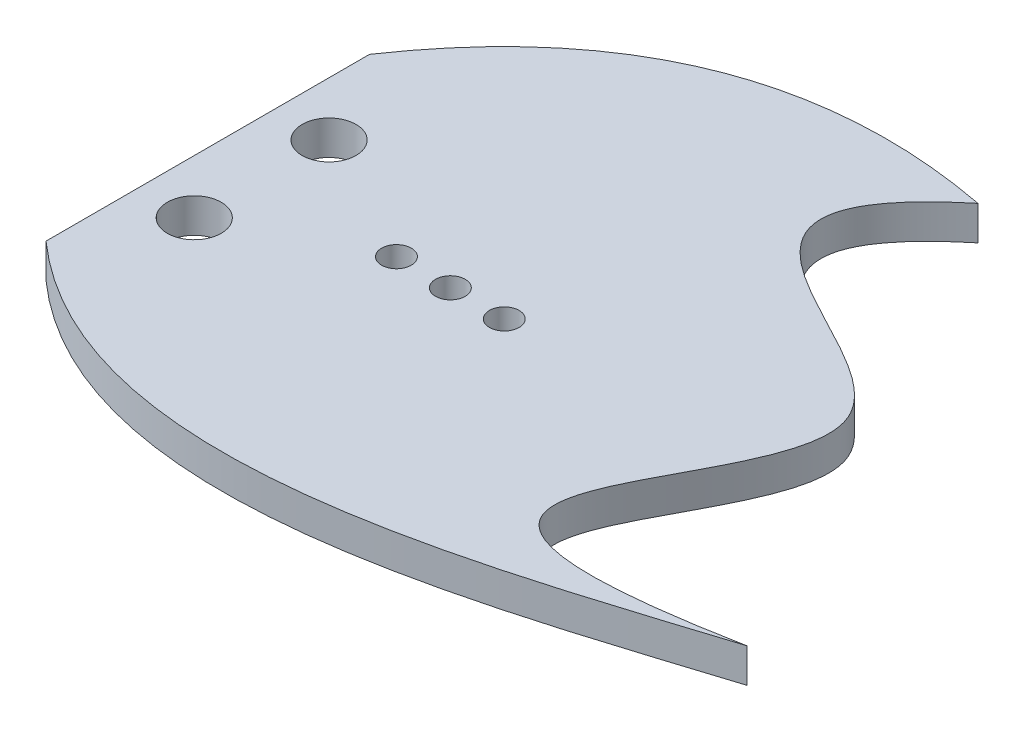
SolidWorks part; units mm, degrees
ref_plane "Front Plane" through (0, 0, 0) normal (0, 0, 1) x (1, 0, 0)
ref_plane "Top Plane" through (0, 0, 0) normal (0, 1, 0) x (1, 0, 0)
ref_plane "Right Plane" through (0, 0, 0) normal (1, 0, 0) x (0, 0, -1)
sketch "Sketch2" plane through (0, 0, 0) normal (0, 1, 0) x (1, 0, 0)
  line L0 (56.3918, 108.1514) -> (56.3918, 48.1514)
  spline S0 degree 2 poles (56.3918, 108.1514) (85.0564, 150.5532) (136.7606, 140.646) knots 0 0 0 1 1 1
  spline S1 degree 3 poles (56.3918, 48.1514) (92.6532, 15.9657) (146.2241, 35.5513) (186.3918, 48.1514) knots 0 0 0 0 1 1 1 1
  spline S2 degree 3 poles (186.3918, 48.1514) (110.317, 33.4597) (213.9084, 108.5176) (101.7916, 111.9077) (136.7606, 140.646) knots 0 0 0 0 0.539021 1 1 1 1
  dimension "D1" = 130
  dimension "D2" = 60
  dimension "D3" = 48.1514
  dimension "D4" = 56.3918
extrude "Boss-Extrude1" add sketch "Sketch2" along normal blind 6.35
sketch "Sketch3" plane through (0, 0, 0) normal (0, 1, 0) x (1, 0, 0)
  line L0 (56.3918, 108.1514) -> (56.3918, 48.1514) construction
  circle A0 centre (101.3918, 78.1514) radius 2.75
  point P4 (0, 0)
  dimension "D2" = 5.5
  dimension "D1" = 45
  dimension "D3" = 30
extrude "Cut-Extrude1" cut sketch "Sketch3" along normal blind 6.35
sketch "Sketch4" plane through (0, 0, 0) normal (0, 1, 0) x (1, 0, 0)
  circle A0 centre (66.3918, 90.6514) radius 5
  circle A1 centre (66.3918, 65.6514) radius 5
  dimension "D3" = 10
  dimension "D4" = 10
  dimension "D1" = 17.5
  dimension "D2" = 42.5
extrude "Cut-Extrude2" cut sketch "Sketch4" along normal blind 6.35
sketch "Sketch5" plane through (0, 0, 0) normal (0, 1, 0) x (1, 0, 0)
  circle A0 centre (101.3918, 78.1514) radius 2.75
  circle A1 centre (111.3918, 78.1514) radius 2.75
  circle A2 centre (91.3918, 78.1514) radius 2.75
  dimension "D1" = 10
  dimension "D2" = 10
extrude "Cut-Extrude3" cut sketch "Sketch5" along normal blind 6.35
